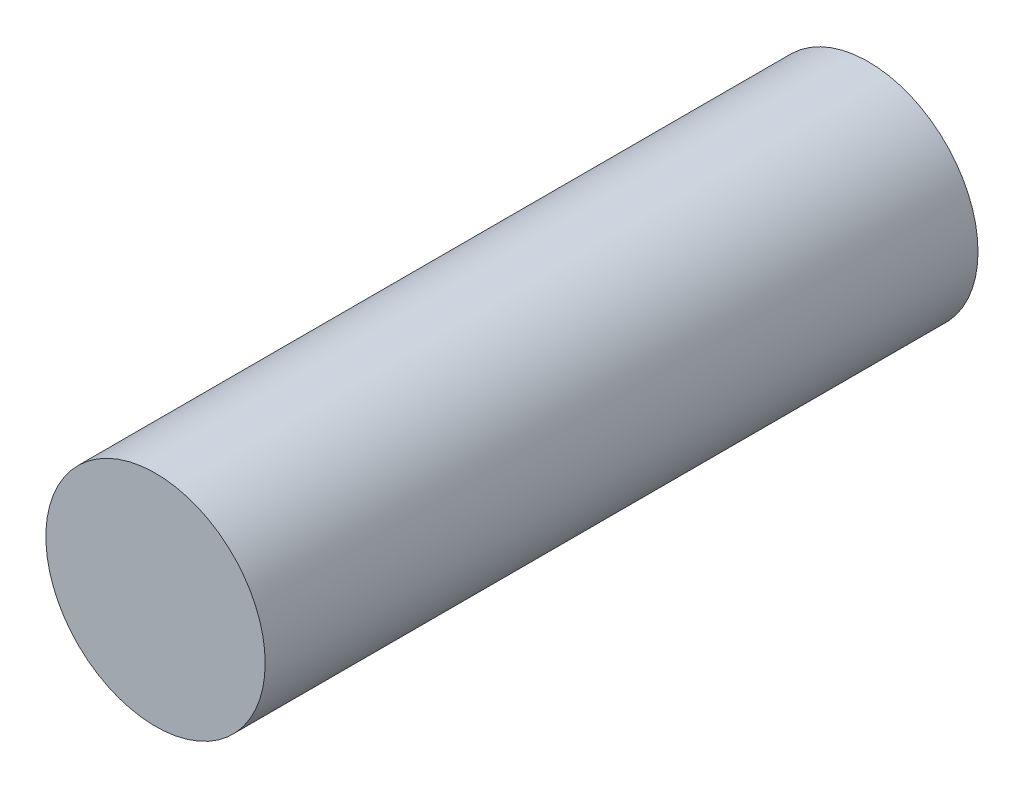
SolidWorks part; units mm, degrees
ref_plane "Front Plane" through (0, 0, 0) normal (0, 0, 1) x (1, 0, 0)
ref_plane "Top Plane" through (0, 0, 0) normal (0, 1, 0) x (1, 0, 0)
ref_plane "Right Plane" through (0, 0, 0) normal (1, 0, 0) x (0, 0, -1)
sketch "Sketch1" plane through (0, 0, 0) normal (0, 0, 1) x (1, 0, 0)
  circle A0 centre (0, 0) radius 2
  dimension "D1" = 4
extrude "Boss-Extrude1" add sketch "Sketch1" along normal blind 13
